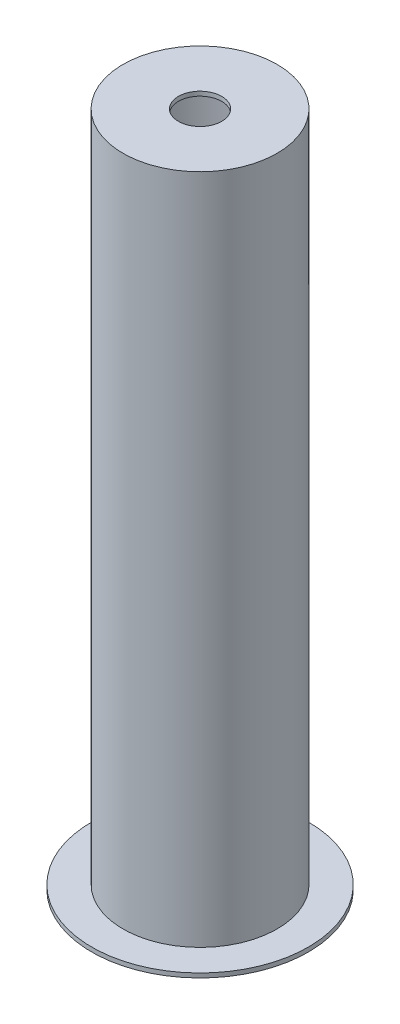
SolidWorks part; units mm, degrees
ref_plane "Plano frontal" through (0, 0, 0) normal (0, 0, 1) x (1, 0, 0)
ref_plane "Plano superior" through (0, 0, 0) normal (0, 1, 0) x (1, 0, 0)
ref_plane "Plano direito" through (0, 0, 0) normal (1, 0, 0) x (0, 0, -1)
sketch "Esboço1" plane through (0, 0, 0) normal (0, 0, 1) x (1, 0, 0)
  line L0 (0, 0) -> (0, 1560) construction
  line L1 (0, 0) -> (457.6466, 0) construction
  line L2 (50, 1560) -> (177.8, 1560)
  line L3 (177.8, 1560) -> (177.8, 10)
  line L4 (177.8, 10) -> (250, 10)
  line L5 (250, 10) -> (250, 0)
  line L6 (170, 0) -> (250, 0)
  line L7 (173.02, 10) -> (173.02, 1550)
  line L8 (173.02, 1550) -> (50, 1550)
  line L9 (173.02, 10) -> (170, 10)
  line L10 (50, 1560) -> (50, 1550)
  line L11 (170, 10) -> (170, 0)
  dimension "D1" = 355.6
  dimension "D2" = 4.78
  dimension "D3" = 10
  dimension "D4" = 10
  dimension "D5" = 1560
  dimension "D6" = 500
  dimension "D7" = 100
  dimension "D8" = 10
  dimension "D9" = 340
revolve "Revolução1" add sketch "Esboço1" angle 360 about L0
